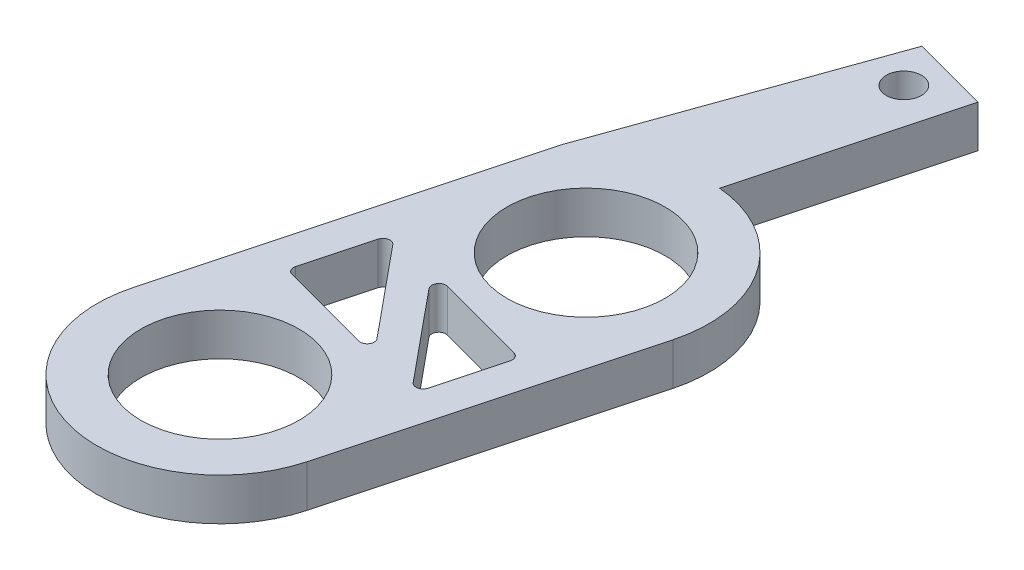
SolidWorks part; units mm, degrees
ref_plane "Front Plane" through (0, 0, 0) normal (0, 0, 1) x (1, 0, 0)
ref_plane "Top Plane" through (0, 0, 0) normal (0, 1, 0) x (1, 0, 0)
ref_plane "Right Plane" through (0, 0, 0) normal (1, 0, 0) x (0, 0, -1)
sketch "Sketch1" plane through (0, 0, 0) normal (0, 1, 0) x (1, 0, 0)
  line L0 (7.4979, -57.8881) -> (21.4677, -5.7523)
  line L1 (-35.4375, -46.3836) -> (-19.0441, 14.7971)
  line L2 (0, 0) -> (-13.9698, -52.1358) construction
  line L3 (0, -52.1358) -> (0, 0) construction
  line L4 (-1.9527, 62.6357) -> (11.8479, 58.9378)
  line L6 (11.8479, 58.9378) -> (1.9869, 22.136)
  line L9 (-19.0441, 14.7971) -> (-1.9527, 62.6357)
  circle A0 centre (0, 0) radius 23.8125 construction
  circle A1 centre (-13.9698, -52.1358) radius 23.8125 construction
  circle A2 centre (-13.9698, -52.1358) radius 14.2875
  circle A3 centre (0, 0) radius 14.2875
  arc A4 (-35.4375, -46.3836) -> (7.4979, -57.8881) centre (-13.9698, -52.1358) ccw
  arc A5 (21.4677, -5.7523) -> (1.9869, 22.136) centre (0, 0) ccw
  circle A6 centre (-13.9698, -52.1358) radius 22.225 construction
  circle A8 centre (0, 0) radius 22.225 construction
  dimension "D1" = 47.625
  dimension "D2" = 28.575
  dimension "D3" = 28.575
  dimension "D4" = 44.45
  dimension "D7" = 18.415
  dimension "D8" = 14.2875
  dimension "D5" = 53.975
  dimension "D6" = 15
  dimension "D9" = 50.8
  dimension "D10" = 38.1
extrude "Boss-Extrude1" add sketch "Sketch1" along normal blind 7.62
sketch "Sketch2" plane through (0, 7.62, 0) normal (0, 1, 0) x (1, 0, 0)
  line L0 (-26.8143, -20.7546) -> (14.4828, -31.8202) construction
  line L1 (-19.0441, 14.7971) -> (-35.4375, -46.3836) construction
  line L2 (7.4979, -57.8881) -> (21.4677, -5.7523) construction
  line L3 (-20.2658, -14.2918) -> (-2.9068, -35.3781)
  line L4 (-2.9068, -35.3781) -> (-24.3745, -29.6259)
  line L5 (-24.3745, -29.6259) -> (-20.2658, -14.2918)
  line L6 (-11.0641, -16.7574) -> (10.4036, -22.5096)
  line L7 (10.4036, -22.5096) -> (6.2948, -37.8437)
  line L8 (6.2948, -37.8437) -> (-11.0641, -16.7574)
  line L9 (-19.0441, 14.7971) -> (-35.4375, -46.3836) construction
  dimension "D1" = 6.3488
  dimension "D2" = 22.225
  dimension "D3" = 15.875
  dimension "D4" = 6.35
extrude "Cut-Extrude1" cut sketch "Sketch2" against normal through all
fillet "Fillet1" radius 1.27 6 edges at (6.2948, 3.81, 37.8437) (10.4036, 3.81, 22.5096) (-11.0641, 3.81, 16.7574) (-20.2658, 3.81, 14.2918) (-24.3745, 3.81, 29.6259) (-2.9068, 3.81, 35.3781)
sketch "Sketch3" plane through (0, 7.62, 0) normal (0, 1, 0) x (1, 0, 0)
  line L0 (1.9869, 22.136) -> (11.8479, 58.9378) construction
  line L2 (11.8479, 58.9378) -> (-1.9527, 62.6357) construction
  circle A0 centre (2.5374, 54.8585) radius 3.175
  point P6 (5.142, 60.1161)
  dimension "D1" = 6.35
  dimension "D2" = 7.9375
  dimension "D3" = 6.35
extrude "Cut-Extrude2" cut sketch "Sketch3" against normal up to surface (7.62 mm away) up to face at (2.476, 0, 25.8209)
ref_plane "Plane1" through (1.9869, 7.62, -22.136) normal (0.2588, 0, -0.9659) x (-0.9659, 0, -0.2588)
